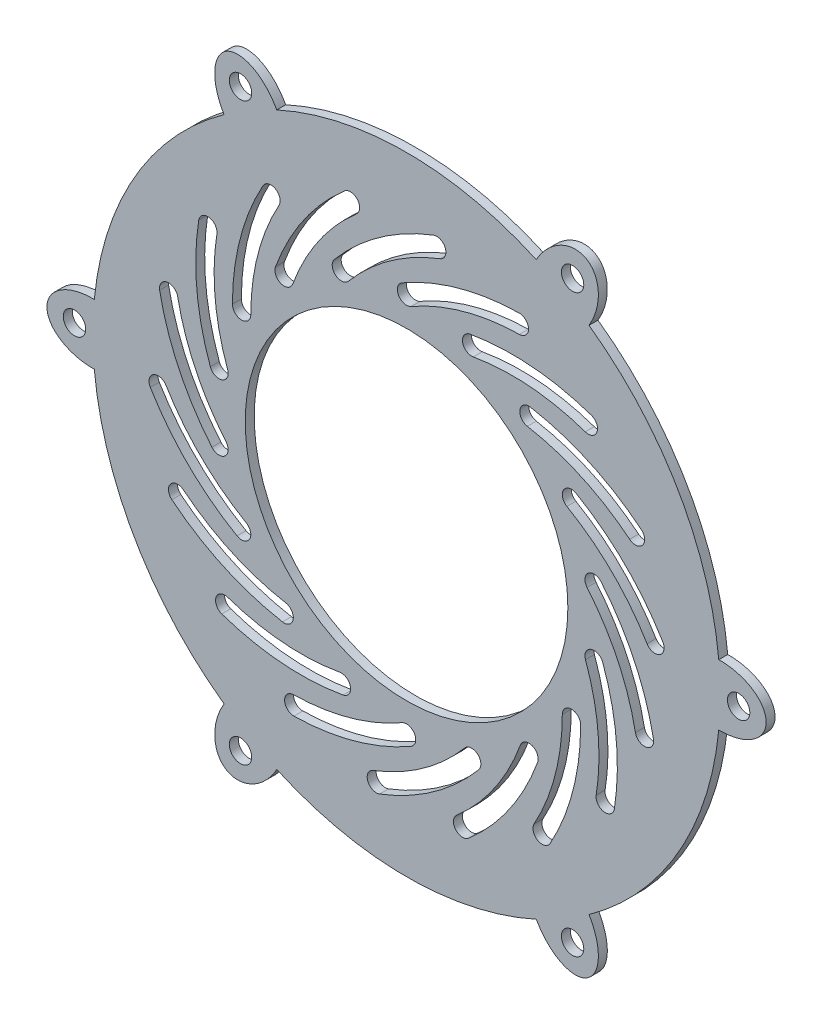
SolidWorks part; units mm, degrees
ref_plane "Front Plane" through (0, 0, 0) normal (0, 0, 1) x (1, 0, 0)
ref_plane "Top Plane" through (0, 0, 0) normal (0, 1, 0) x (1, 0, 0)
ref_plane "Right Plane" through (0, 0, 0) normal (1, 0, 0) x (0, 0, -1)
sketch "Sketch1" plane through (0, 0, 0) normal (0, 0, 1) x (1, 0, 0)
  line L0 (0, 0) -> (-63, 0) construction
  circle A0 centre (0, 0) radius 36
  arc A1 (-69.6738, -6.75) -> (-40.7174, -56.9394) centre (0, 0) ccw
  arc A2 (-40.7174, 56.9394) -> (-69.6738, 6.75) centre (0, 0) ccw
  arc A3 (28.9523, 63.732) -> (-28.9523, 63.732) centre (0, 0) ccw
  arc A4 (69.6697, 6.7926) -> (40.7174, 56.9394) centre (0, 0) ccw
  arc A5 (40.7174, -56.9394) -> (69.6697, -6.7926) centre (0, 0) ccw
  arc A6 (-28.9523, -63.732) -> (28.9523, -63.732) centre (0, 0) ccw
  ellipse E0 centre (-70, 0) end of major axis (-59.75, 0) minor radius 6.7534 (-69.6738, 6.75) -> (-69.6738, -6.75) ccw
  ellipse E1 centre (-35, 60.6218) end of major axis (-40.119, 69.4882) minor radius 6.7961 (-28.9523, 63.732) -> (-40.7174, 56.9394) ccw
  ellipse E2 centre (35, 60.6218) end of major axis (40.119, 69.4882) minor radius 6.7961 (40.7174, 56.9394) -> (28.9523, 63.732) ccw
  ellipse E3 centre (70, 0) end of major axis (59.762, 0) minor radius 6.7961 (69.6697, -6.7926) -> (69.6697, 6.7926) ccw
  ellipse E4 centre (35, -60.6218) end of major axis (29.881, -51.7554) minor radius 6.7961 (28.9523, -63.732) -> (40.7174, -56.9394) ccw
  ellipse E5 centre (-35, -60.6218) end of major axis (-29.881, -51.7554) minor radius 6.7961 (-40.7174, -56.9394) -> (-28.9523, -63.732) ccw
  point P48 (0, 0)
  dimension "D1" = 72
  dimension "D2" = 140
  dimension "D3" = 13.5
  dimension "D4" = 20.5
extrude "Boss-Extrude1" add sketch "Sketch1" along normal blind 2
sketch "Sketch2" plane through (0, 0, 0) normal (0, 0, 1) x (1, 0, 0)
  line L0 (0, 0) -> (0, 70) construction
  line L1 (0, 42.5) -> (9.8119, 48.1649) construction
  line L2 (0, 0) -> (0, 42.5) construction
  circle A0 centre (0, 0) radius 70 construction
  circle A1 centre (0, 0) radius 42.5 construction
  circle A2 centre (0, 0) radius 55.5 construction
  arc A3 (0, 42.5) -> (25.1662, 49.4663) centre (26.025, -2.5766) cw construction
  arc A4 (25.1323, 51.516) -> (-1.025, 44.2754) centre (26.025, -2.5766) ccw
  arc A5 (25.2, 47.4166) -> (1.025, 40.7246) centre (26.025, -2.5766) ccw
  arc A6 (25.2, 47.4166) -> (25.1323, 51.516) centre (25.1662, 49.4663) ccw
  arc A7 (-1.025, 44.2754) -> (1.025, 40.7246) centre (0, 42.5) ccw
  arc A8 (14.5359, 39.9369) -> (40.5669, 37.8758) centre (23.5742, -11.3223) cw construction
  arc A9 (41.2362, 39.8134) -> (14.1799, 41.9558) centre (23.5742, -11.3223) ccw
  arc A10 (39.8977, 35.9381) -> (14.8918, 37.9181) centre (23.5742, -11.3223) ccw
  arc A11 (39.8977, 35.9381) -> (41.2362, 39.8134) centre (40.5669, 37.8758) ccw
  arc A12 (14.1799, 41.9558) -> (14.8918, 37.9181) centre (14.5359, 39.9369) ccw
  arc A13 (27.3185, 32.5569) -> (51.0747, 21.7169) centre (18.2801, -18.7024) cw construction
  arc A14 (52.3663, 23.3088) -> (27.6745, 34.5757) centre (18.2801, -18.7024) ccw
  arc A15 (49.7831, 20.125) -> (26.9625, 30.538) centre (18.2801, -18.7024) ccw
  arc A16 (49.7831, 20.125) -> (52.3663, 23.3088) centre (51.0747, 21.7169) ccw
  arc A17 (27.6745, 34.5757) -> (26.9625, 30.538) centre (27.3185, 32.5569) ccw
  arc A18 (36.8061, 21.25) -> (55.4221, 2.9386) centre (10.7811, -23.8266) cw construction
  arc A19 (57.1803, 3.9928) -> (37.8311, 23.0254) centre (10.7811, -23.8266) ccw
  arc A20 (53.664, 1.8845) -> (35.7811, 19.4746) centre (10.7811, -23.8266) ccw
  arc A21 (53.664, 1.8845) -> (57.1803, 3.9928) centre (55.4221, 2.9386) ccw
  arc A22 (37.8311, 23.0254) -> (35.7811, 19.4746) centre (36.8061, 21.25) ccw
  arc A23 (41.8543, 7.38) -> (53.0848, -16.1941) centre (1.9817, -26.077) cw construction
  arc A24 (55.0976, -15.8049) -> (43.4247, 8.6978) centre (1.9817, -26.077) ccw
  arc A25 (51.0721, -16.5833) -> (40.2839, 6.0623) centre (1.9817, -26.077) ccw
  arc A26 (51.0721, -16.5833) -> (55.0976, -15.8049) centre (53.0848, -16.1941) ccw
  arc A27 (43.4247, 8.6978) -> (40.2839, 6.0623) centre (41.8543, 7.38) ccw
  arc A28 (41.8543, -7.38) -> (44.3447, -33.3736) centre (-7.0567, -25.1822) cw construction
  arc A29 (46.3692, -33.6962) -> (43.7807, -6.6789) centre (-7.0567, -25.1822) ccw
  arc A30 (42.3203, -33.0509) -> (39.928, -8.0812) centre (-7.0567, -25.1822) ccw
  arc A31 (42.3203, -33.0509) -> (46.3692, -33.6962) centre (44.3447, -33.3736) ccw
  arc A32 (43.7807, -6.6789) -> (39.928, -8.0812) centre (41.8543, -7.38) ccw
  arc A33 (36.8061, -21.25) -> (30.256, -46.5277) centre (-15.2439, -21.25) cw construction
  arc A34 (32.048, -47.5233) -> (38.8561, -21.25) centre (-15.2439, -21.25) ccw
  arc A35 (28.464, -45.5321) -> (34.7561, -21.25) centre (-15.2439, -21.25) ccw
  arc A36 (28.464, -45.5321) -> (32.048, -47.5233) centre (30.256, -46.5277) ccw
  arc A37 (38.8561, -21.25) -> (34.7561, -21.25) centre (36.8061, -21.25) ccw
  arc A38 (27.3185, -32.5569) -> (12.5179, -54.0699) centre (-21.5925, -14.7547) cw construction
  arc A39 (13.8614, -55.6183) -> (29.2448, -33.258) centre (-21.5925, -14.7547) ccw
  arc A40 (11.1745, -52.5214) -> (25.3921, -31.8557) centre (-21.5925, -14.7547) ccw
  arc A41 (11.1745, -52.5214) -> (13.8614, -55.6183) centre (12.5179, -54.0699) ccw
  arc A42 (29.2448, -33.258) -> (25.3921, -31.8557) centre (27.3185, -32.5569) ccw
  arc A43 (14.5359, -39.9369) -> (-6.73, -55.0904) centre (-25.3368, -6.4798) cw construction
  arc A44 (-5.9972, -57.005) -> (16.1062, -41.2547) centre (-25.3368, -6.4798) ccw
  arc A45 (-7.4628, -53.1759) -> (12.9655, -38.6192) centre (-25.3368, -6.4798) ccw
  arc A46 (-7.4628, -53.1759) -> (-5.9972, -57.005) centre (-6.73, -55.0904) ccw
  arc A47 (16.1062, -41.2547) -> (12.9655, -38.6192) centre (14.5359, -39.9369) ccw
  arc A48 (0, -42.5) -> (-25.1662, -49.4663) centre (-26.025, 2.5766) cw construction
  arc A49 (-25.1323, -51.516) -> (1.025, -44.2754) centre (-26.025, 2.5766) ccw
  arc A50 (-25.2, -47.4166) -> (-1.025, -40.7246) centre (-26.025, 2.5766) ccw
  arc A51 (-25.2, -47.4166) -> (-25.1323, -51.516) centre (-25.1662, -49.4663) ccw
  arc A52 (1.025, -44.2754) -> (-1.025, -40.7246) centre (0, -42.5) ccw
  arc A53 (-14.5359, -39.9369) -> (-40.5669, -37.8758) centre (-23.5742, 11.3223) cw construction
  arc A54 (-41.2362, -39.8134) -> (-14.1799, -41.9558) centre (-23.5742, 11.3223) ccw
  arc A55 (-39.8977, -35.9381) -> (-14.8918, -37.9181) centre (-23.5742, 11.3223) ccw
  arc A56 (-39.8977, -35.9381) -> (-41.2362, -39.8134) centre (-40.5669, -37.8758) ccw
  arc A57 (-14.1799, -41.9558) -> (-14.8918, -37.9181) centre (-14.5359, -39.9369) ccw
  arc A58 (-27.3185, -32.5569) -> (-51.0747, -21.7169) centre (-18.2801, 18.7024) cw construction
  arc A59 (-52.3663, -23.3088) -> (-27.6745, -34.5757) centre (-18.2801, 18.7024) ccw
  arc A60 (-49.7831, -20.125) -> (-26.9625, -30.538) centre (-18.2801, 18.7024) ccw
  arc A61 (-49.7831, -20.125) -> (-52.3663, -23.3088) centre (-51.0747, -21.7169) ccw
  arc A62 (-27.6745, -34.5757) -> (-26.9625, -30.538) centre (-27.3185, -32.5569) ccw
  arc A63 (-36.8061, -21.25) -> (-55.4221, -2.9386) centre (-10.7811, 23.8266) cw construction
  arc A64 (-57.1803, -3.9928) -> (-37.8311, -23.0254) centre (-10.7811, 23.8266) ccw
  arc A65 (-53.664, -1.8845) -> (-35.7811, -19.4746) centre (-10.7811, 23.8266) ccw
  arc A66 (-53.664, -1.8845) -> (-57.1803, -3.9928) centre (-55.4221, -2.9386) ccw
  arc A67 (-37.8311, -23.0254) -> (-35.7811, -19.4746) centre (-36.8061, -21.25) ccw
  arc A68 (-41.8543, -7.38) -> (-53.0848, 16.1941) centre (-1.9817, 26.077) cw construction
  arc A69 (-55.0976, 15.8049) -> (-43.4247, -8.6978) centre (-1.9817, 26.077) ccw
  arc A70 (-51.0721, 16.5833) -> (-40.2839, -6.0623) centre (-1.9817, 26.077) ccw
  arc A71 (-51.0721, 16.5833) -> (-55.0976, 15.8049) centre (-53.0848, 16.1941) ccw
  arc A72 (-43.4247, -8.6978) -> (-40.2839, -6.0623) centre (-41.8543, -7.38) ccw
  arc A73 (-41.8543, 7.38) -> (-44.3447, 33.3736) centre (7.0567, 25.1822) cw construction
  arc A74 (-46.3692, 33.6962) -> (-43.7807, 6.6789) centre (7.0567, 25.1822) ccw
  arc A75 (-42.3203, 33.0509) -> (-39.928, 8.0812) centre (7.0567, 25.1822) ccw
  arc A76 (-42.3203, 33.0509) -> (-46.3692, 33.6962) centre (-44.3447, 33.3736) ccw
  arc A77 (-43.7807, 6.6789) -> (-39.928, 8.0812) centre (-41.8543, 7.38) ccw
  arc A78 (-36.8061, 21.25) -> (-30.256, 46.5277) centre (15.2439, 21.25) cw construction
  arc A79 (-32.048, 47.5233) -> (-38.8561, 21.25) centre (15.2439, 21.25) ccw
  arc A80 (-28.464, 45.5321) -> (-34.7561, 21.25) centre (15.2439, 21.25) ccw
  arc A81 (-28.464, 45.5321) -> (-32.048, 47.5233) centre (-30.256, 46.5277) ccw
  arc A82 (-38.8561, 21.25) -> (-34.7561, 21.25) centre (-36.8061, 21.25) ccw
  arc A83 (-27.3185, 32.5569) -> (-12.5179, 54.0699) centre (21.5925, 14.7547) cw construction
  arc A84 (-13.8614, 55.6183) -> (-29.2448, 33.258) centre (21.5925, 14.7547) ccw
  arc A85 (-11.1745, 52.5214) -> (-25.3921, 31.8557) centre (21.5925, 14.7547) ccw
  arc A86 (-11.1745, 52.5214) -> (-13.8614, 55.6183) centre (-12.5179, 54.0699) ccw
  arc A87 (-29.2448, 33.258) -> (-25.3921, 31.8557) centre (-27.3185, 32.5569) ccw
  arc A88 (-14.5359, 39.9369) -> (6.73, 55.0904) centre (25.3368, 6.4798) cw construction
  arc A89 (5.9972, 57.005) -> (-16.1062, 41.2547) centre (25.3368, 6.4798) ccw
  arc A90 (7.4628, 53.1759) -> (-12.9655, 38.6192) centre (25.3368, 6.4798) ccw
  arc A91 (7.4628, 53.1759) -> (5.9972, 57.005) centre (6.73, 55.0904) ccw
  arc A92 (-16.1062, 41.2547) -> (-12.9655, 38.6192) centre (-14.5359, 39.9369) ccw
  point P11 (12.1391, 47.587)
  point P23 (27.6827, 40.5653)
  point P31 (39.8874, 28.6508)
  point P39 (47.2811, 13.2807)
  point P47 (48.9719, -3.6913)
  point P55 (44.7561, -20.2181)
  point P63 (35.142, -34.3063)
  point P71 (21.2892, -44.2566)
  point P79 (4.8686, -48.8689)
  point P87 (-12.1391, -47.587)
  point P95 (-27.6827, -40.5653)
  point P103 (-39.8874, -28.6508)
  point P111 (-47.2811, -13.2807)
  point P119 (-48.9719, 3.6913)
  point P127 (-44.7561, 20.2181)
  point P135 (-35.142, 34.3063)
  point P143 (-21.2892, 44.2566)
  point P151 (-4.8686, 48.8689)
  dimension "D1" = 85
  dimension "D2" = 111
  dimension "D3" = 50
  dimension "D4" = 2.05
  dimension "D5" = 60
  dimension "D6" = 18
  dimension "D7" = 42.5
extrude "Cut-Extrude3" cut sketch "Sketch2" along normal through all
sketch "Sketch6" plane through (0, 0, 0) normal (0, 0, 1) x (1, 0, 0)
  circle A0 centre (-74.0989, 0) radius 2.5
  dimension "D1" = 5
extrude "Cut-Extrude4" cut sketch "Sketch6" along normal through all
pattern_circular "CirPattern1" count 6 over 360 about axis through (0, 0, 0) along (0, 0, 1) of "Cut-Extrude4"
